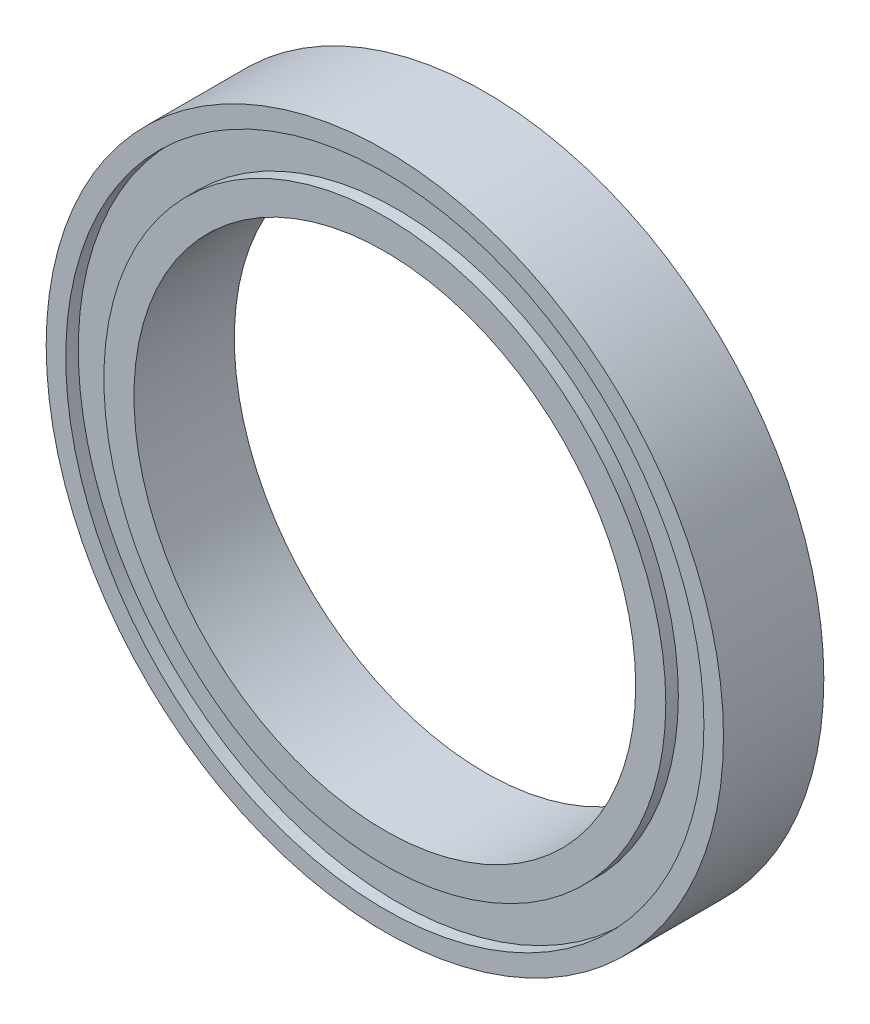
SolidWorks part; units mm, degrees
material "鋅合金 7; AG40B; Zn-4Al-0.015Mg"
ref_plane "前基準面" through (0, 0, 0) normal (0, 0, 1) x (1, 0, 0)
ref_plane "上基準面" through (0, 0, 0) normal (0, 1, 0) x (1, 0, 0)
ref_plane "右基準面" through (0, 0, 0) normal (1, 0, 0) x (0, 0, -1)
sketch "草圖1" plane through (0, 0, 0) normal (0, 0, 1) x (1, 0, 0)
  circle A0 centre (0, 0) radius 10
  circle A1 centre (0, 0) radius 13.5
  dimension "D1" = 27
  dimension "D2" = 20
extrude "填料-伸長1" add sketch "草圖1" along normal blind 4
sketch "草圖2" plane through (0, 0, 4) normal (0, 0, 1) x (1, 0, 0)
  circle A0 centre (0, 0) radius 11.2
  circle A1 centre (0, 0) radius 12.72
  dimension "D1" = 22.4
  dimension "D2" = 25.44
extrude "除料-伸長1" cut sketch "草圖2" against normal blind 0.5
sketch "草圖3" plane through (0, 0, 0) normal (0, 0, -1) x (-1, 0, 0)
  circle A0 centre (0, 0) radius 11.2
  circle A1 centre (0, 0) radius 12.72
  dimension "D1" = 22.4
  dimension "D2" = 25.44
extrude "除料-伸長2" cut sketch "草圖3" against normal blind 0.5
